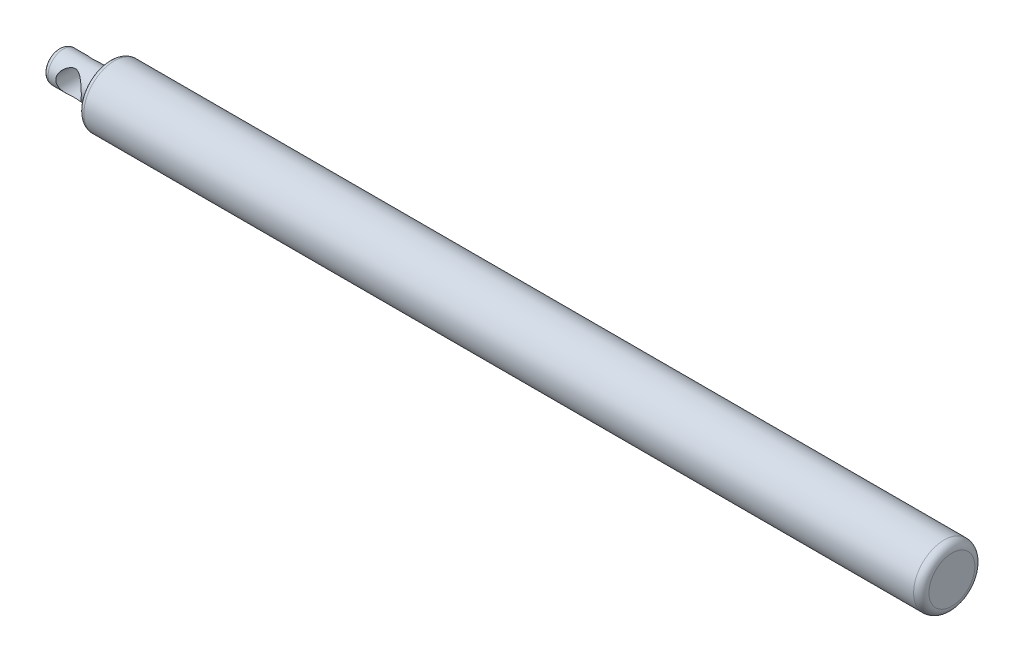
SolidWorks part; units mm, degrees
ref_plane "Front Plane" through (0, 0, 0) normal (0, 0, 1) x (1, 0, 0)
ref_plane "Top Plane" through (0, 0, 0) normal (0, 1, 0) x (1, 0, 0)
ref_plane "Right Plane" through (0, 0, 0) normal (1, 0, 0) x (0, 0, -1)
sketch "Sketch1" plane through (0, 0, 0) normal (0, 0, 1) x (1, 0, 0)
  line L0 (0, 0) -> (175, 0) construction
  line L1 (0, 3) -> (10, 3)
  line L2 (10, 3) -> (10, 6)
  line L3 (10, 6) -> (175, 6)
  line L4 (175, 6) -> (175, 0)
  line L5 (0, 3) -> (0, 0)
  line L6 (0, 0) -> (175, 0)
  dimension "D1" = 10
  dimension "D2" = 165
  dimension "D3" = 3
  dimension "D4" = 6
revolve "Revolve1" add sketch "Sketch1" angle 360 about L0
sketch "Sketch2" plane through (0, 0, 0) normal (0, 0, 1) x (1, 0, 0)
  circle A0 centre (5, 0) radius 2.5
  dimension "D1" = 5
  dimension "D2" = 5
extrude "Cut-Extrude1" cut sketch "Sketch2" against normal through all both and the other way through all
fillet "Fillet2" radius 1 1 edges at (0, 0, 3)
fillet "Fillet3" radius 1 2 edges at (10, 0, 3) (10, 0, 6)
fillet "Fillet4" radius 1.5 1 edges at (175, 0, 6)
